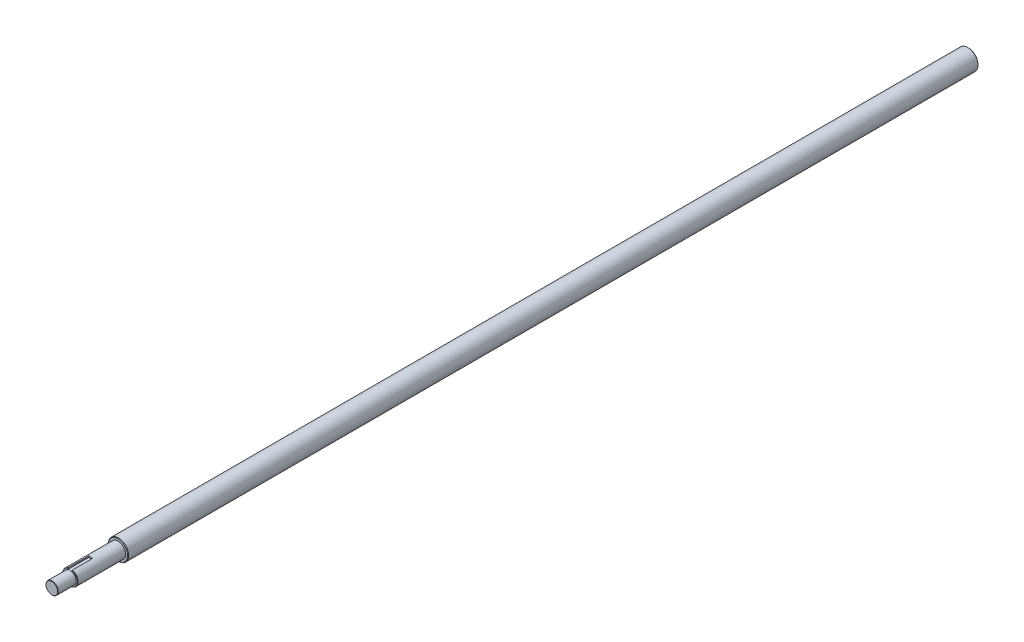
SolidWorks part; units mm, degrees
ref_plane "Płaszczyzna przednia" through (0, 0, 0) normal (0, 0, 1) x (1, 0, 0)
ref_plane "Płaszczyzna górna" through (0, 0, 0) normal (0, 1, 0) x (1, 0, 0)
ref_plane "Płaszczyzna prawa" through (0, 0, 0) normal (1, 0, 0) x (0, 0, -1)
sketch "Szkic1" plane through (0, 0, 0) normal (0, 0, 1) x (1, 0, 0)
  circle A0 centre (0, 0) radius 10
extrude "Dodanie-wyciągnięcie1" add sketch "Szkic1" along normal blind 900
cosmetic thread "Oznaczenie gwintu4" parameters "D1"=1119, "D2"=17.252
sketch "Szkic2" plane through (0, 0, 900) normal (0, 0, 1) x (1, 0, 0)
  circle A1 centre (0, 0) radius 10
  circle A2 centre (0, 0) radius 7.5
  dimension "D1" = 20
  dimension "D2" = 15
extrude "Wytnij-wyciągnięcie1" cut sketch "Szkic2" against normal blind 65
cosmetic thread "Oznaczenie gwintu5" parameters "D1"=20, "D2"=13.891
sketch "Szkic3" plane through (0, 0, 900) normal (0, 0, 1) x (1, 0, 0)
  circle A0 centre (0, 0) radius 6
  circle A1 centre (0, 0) radius 10
  point P4 (0, 0)
  dimension "D1" = 12
  dimension "D2" = 20
extrude "Wytnij-wyciągnięcie2" cut sketch "Szkic3" against normal blind 18
chamfer "Sfazowanie1" distance 0.5 angle 45 1 edges at (10, 0, 835)
chamfer "Sfazowanie2" distance 0.3 angle 45 2 edges at (6, 0, 900) (7.5, 0, 882)
chamfer "Sfazowanie3" distance 0.5 angle 45 1 edges at (10, 0, 0)
sketch "Szkic4" plane through (0, 0, 882) normal (0, 0, 1) x (1, 0, 0)
  line L0 (0, 0) -> (0, 6) construction
  line L1 (0, 6) -> (2, 6)
  line L2 (2, 6) -> (2, 8.058)
  line L3 (2, 8.058) -> (-2, 8.058)
  line L4 (-2, 8.058) -> (-2, 6)
  line L5 (-2, 6) -> (0, 6)
  circle A1 centre (0, 0) radius 6 construction
extrude "Wytnij-wyciągnięcie3" cut sketch "Szkic4" against normal blind 20
